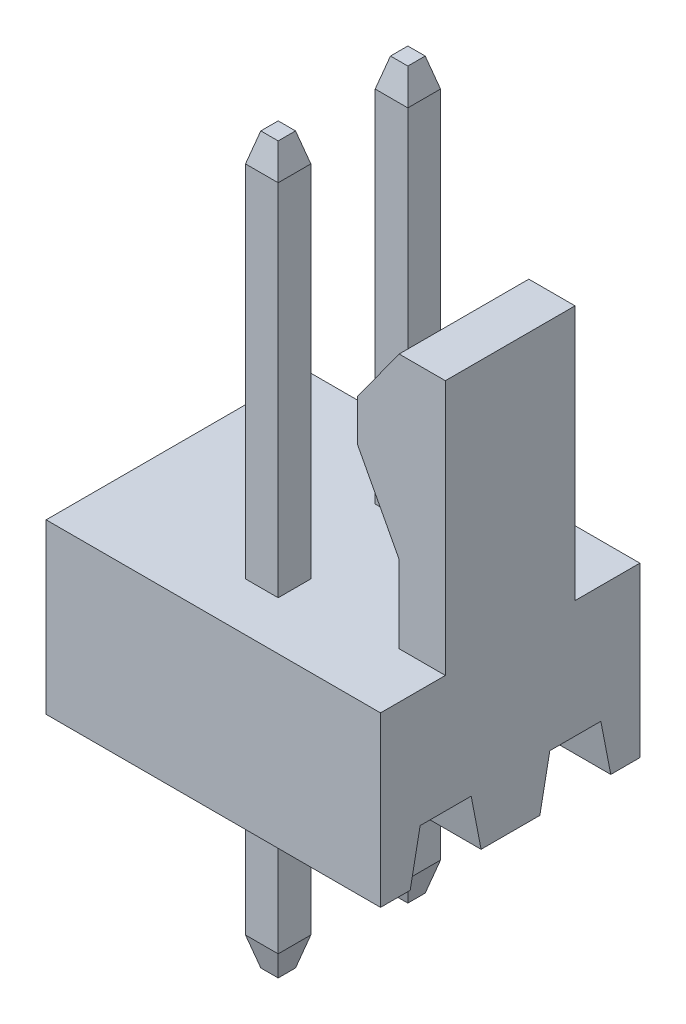
SolidWorks part; units mm, degrees
ref_plane "Alzado" through (0, 0, 0) normal (0, 0, 1) x (1, 0, 0)
ref_plane "Planta" through (0, 0, 0) normal (0, 1, 0) x (1, 0, 0)
ref_plane "Vista lateral" through (0, 0, 0) normal (1, 0, 0) x (0, 0, -1)
sketch "Croquis1" plane through (0, 0, 0) normal (0, 0, 1) x (1, 0, 0)
  line L0 (0, 0) -> (6.55, 0)
  line L1 (6.55, 0) -> (6.55, 8.3)
  line L2 (6.55, 8.3) -> (5.6448, 8.3)
  line L3 (5.6448, 8.3) -> (4.8278, 7.1708)
  line L4 (4.8278, 7.1708) -> (4.8278, 6.3605)
  line L5 (4.8278, 6.3605) -> (5.6448, 4.8144)
  line L6 (5.6448, 4.8144) -> (5.6448, 3.3)
  line L7 (5.6448, 3.3) -> (0, 3.3)
  line L8 (0, 3.3) -> (0, 0)
  dimension "D1" = 6.55
  dimension "D2" = 3.3
  dimension "D3" = 8.3
extrude "Saliente-Extruir1" add sketch "Croquis1" along normal blind 5.08
sketch "Croquis2" plane through (5.6448, 0, 0) normal (-1, 0, 0) x (0, 0, 1)
  line L0 (0, 3.3) -> (0, 8.3)
  line L1 (0, 8.3) -> (1.27, 8.3)
  line L2 (5.08, 8.3) -> (0, 8.3) construction
  line L3 (1.27, 8.3) -> (1.27, 3.3)
  line L4 (5.08, 3.3) -> (0, 3.3) construction
  line L5 (1.27, 3.3) -> (0, 3.3)
  line L6 (5.08, 8.3) -> (5.08, 3.3)
  line L7 (5.08, 3.3) -> (3.81, 3.3)
  line L8 (3.81, 3.3) -> (3.81, 8.3)
  line L9 (3.81, 8.3) -> (5.08, 8.3)
  line L10 (2.54, 3.3) -> (2.54, 8.3) construction
  line L11 (5.08, 3.3) -> (0, 3.3) construction
  dimension "D1" = 2.54
  dimension "D2" = 1.27
extrude "Cortar-Extruir1" cut sketch "Croquis2" against normal blind 5.08 and the other way blind 5.08
sketch "Croquis4" plane through (0, 3.3, 0) normal (0, 1, 0) x (1, 0, 0)
  line L0 (3.275, 0) -> (3.275, -5.08) construction
  line L1 (6.55, 0) -> (0, 0) construction
  line L2 (6.55, -5.08) -> (0, -5.08) construction
  line L3 (4.8278, -1.27) -> (3.275, -1.27) construction
  line L4 (4.8278, -3.81) -> (3.275, -3.81) construction
  line L6 (3.595, -0.95) -> (2.955, -0.95)
  line L7 (2.955, -0.95) -> (2.955, -1.59)
  line L8 (2.955, -1.59) -> (3.595, -1.59)
  line L9 (3.595, -1.59) -> (3.595, -0.95)
  line L10 (3.595, -3.49) -> (2.955, -3.49)
  line L11 (2.955, -3.49) -> (2.955, -4.13)
  line L12 (2.955, -4.13) -> (3.595, -4.13)
  line L13 (3.595, -4.13) -> (3.595, -3.49)
  circle A0 centre (3.275, -1.27) radius 0.32 construction
  circle A1 centre (3.275, -3.81) radius 0.32 construction
  dimension "D1" = 0.64
  dimension "D2" = 0.64
extrude "Cortar-Extruir2" cut sketch "Croquis4" against normal blind 5.08
sketch "Croquis5" plane through (0, 0, 0) normal (-1, 0, 0) x (0, 0, 1)
  line L0 (2.54, 3.3) -> (2.54, 0) construction
  line L1 (3.81, 3.3) -> (1.27, 3.3) construction
  line L2 (5.08, 0) -> (0, 0) construction
  line L3 (0, 1) -> (5.08, 1) construction
  line L4 (0, 3.3) -> (0, 0) construction
  line L5 (5.08, 3.3) -> (5.08, 0) construction
  line L6 (1.2644, 1) -> (1.7644, 1)
  line L7 (1.2644, 1) -> (0.7644, 1)
  line L8 (0.7644, 1) -> (0.5701, 0)
  line L9 (1.7644, 1) -> (1.9588, 0)
  line L10 (0.5701, 0) -> (1.9588, 0)
  line L11 (3.3044, 1) -> (3.1101, 0)
  line L12 (3.8044, 1) -> (3.3044, 1)
  line L13 (3.8044, 1) -> (4.3044, 1)
  line L14 (4.3044, 1) -> (4.4988, 0)
  line L15 (3.1101, 0) -> (4.4988, 0)
  dimension "D1" = 1
  dimension "D2" = 0.5
  dimension "D3" = 0.5
  dimension "D4" = 1.2756
  dimension "D5" = 2
extrude "Cortar-Extruir3" cut sketch "Croquis5" against normal blind 15.08
sketch "Croquis6" plane through (0, 3.3, 0) normal (0, 1, 0) x (1, 0, 0)
  line L1 (3.595, -0.95) -> (2.955, -0.95)
  line L2 (2.955, -0.95) -> (2.955, -1.59)
  line L3 (2.955, -1.59) -> (3.595, -1.59)
  line L4 (3.595, -1.59) -> (3.595, -0.95)
  line L5 (3.595, -3.49) -> (2.955, -3.49)
  line L6 (2.955, -3.49) -> (2.955, -4.13)
  line L7 (2.955, -4.13) -> (3.595, -4.13)
  line L8 (3.595, -4.13) -> (3.595, -3.49)
  circle A0 centre (3.275, -1.27) radius 0.32 construction
  circle A1 centre (3.275, -3.81) radius 0.32 construction
extrude "Saliente-Extruir2" add sketch "Croquis6" along normal blind 7.6 and the other way blind 6.6
chamfer "Chaflán1" distance 0.15 angle 75 8 edges at (3.275, 10.9, 1.59) (2.955, 10.9, 1.27) (3.275, 10.9, 0.95) (3.595, 10.9, 1.27) (3.275, 10.9, 4.13) (2.955, 10.9, 3.81) (3.275, 10.9, 3.49) (3.595, 10.9, 3.81)
chamfer "Chaflán2" distance 0.15 angle 75 8 edges at (3.275, -3.3, 0.95) (2.955, -3.3, 1.27) (3.275, -3.3, 1.59) (3.595, -3.3, 1.27) (3.275, -3.3, 3.49) (2.955, -3.3, 3.81) (3.275, -3.3, 4.13) (3.595, -3.3, 3.81)
sketch "Croquis7" plane through (0, -3.3, 0) normal (0, -1, 0) x (1, 0, 0)
  circle A0 centre (3.275, 3.81) radius 0.1087
extrude "Cortar-Extruir4" cut sketch "Croquis7" against normal blind 0.1
